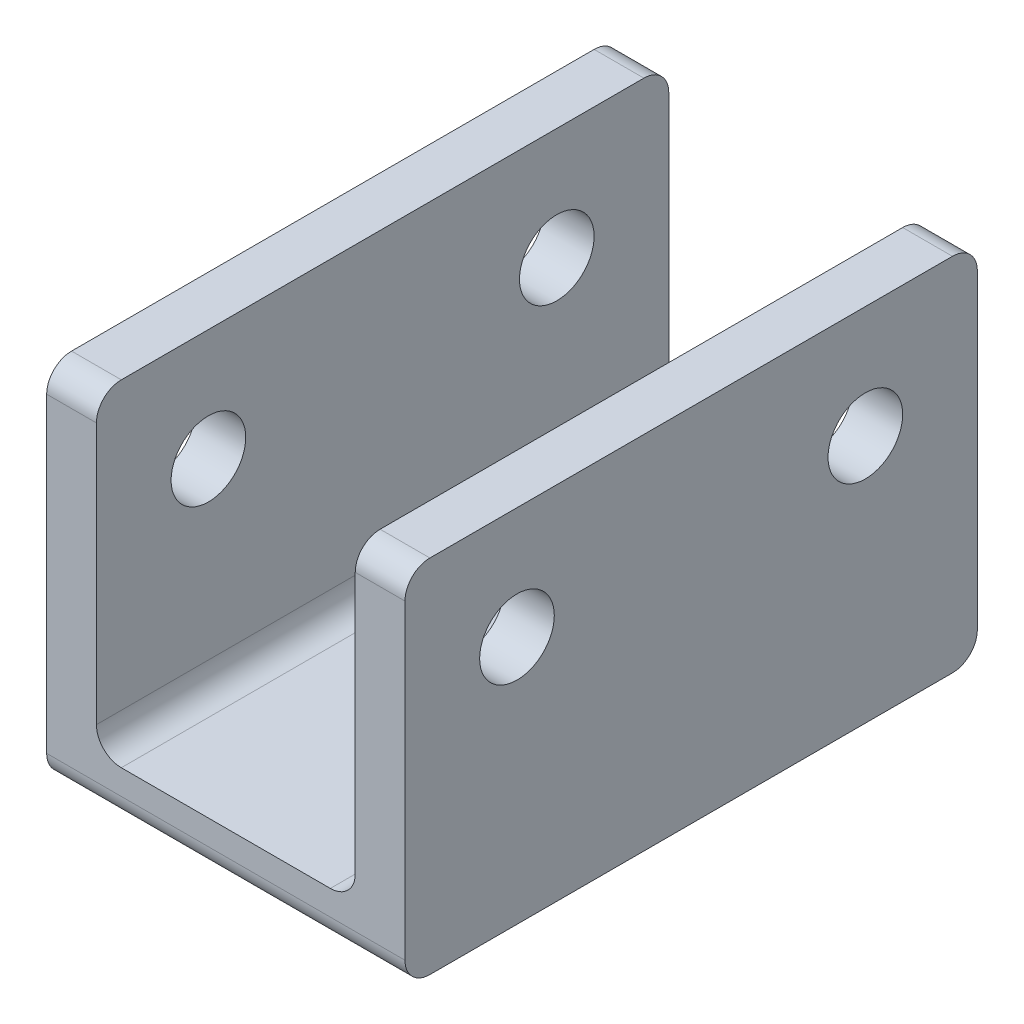
SolidWorks part; units mm, degrees
ref_plane "Front Plane" through (0, 0, 0) normal (0, 0, 1) x (1, 0, 0)
ref_plane "Top Plane" through (0, 0, 0) normal (0, 1, 0) x (1, 0, 0)
ref_plane "Right Plane" through (0, 0, 0) normal (1, 0, 0) x (0, 0, -1)
sketch "Sketch1" plane through (0, 0, 0) normal (0, 0, 1) x (1, 0, 0)
  line L0 (-5.2, 1) -> (5.2, 1)
  line L5 (7.2, -1) -> (-7.2, -1)
  line L6 (-5.2, 1) -> (-5.2, 13.5)
  line L7 (-5.2, 13.5) -> (-7.2, 13.5)
  line L8 (-7.2, 13.5) -> (-7.2, -1)
  line L9 (0, -55) -> (0, 55) construction
  line L10 (7.2, 13.5) -> (7.2, -1)
  line L11 (5.2, 13.5) -> (7.2, 13.5)
  line L12 (5.2, 1) -> (5.2, 13.5)
  point P2 (0, 1)
  point P16 (0, -1)
  dimension "D1" = 1
  dimension "D2" = 1
  dimension "D3" = 2
  dimension "D4" = 14.4
  dimension "D5" = 13.5
extrude "Boss-Extrude1" add sketch "Sketch1" along normal mid plane 23
sketch "Sketch2" plane through (7.2, 0, 0) normal (1, 0, 0) x (0, 0, -1)
  line L0 (0, 7.92) -> (0, -7.92) construction
  line L1 (-11.5, 13.5) -> (11.5, 13.5) construction
  circle A0 centre (-7, 9) radius 1.5
  circle A1 centre (7, 9) radius 1.5
  dimension "D3" = 3
  dimension "D1" = 14
  dimension "D2" = 4.5
extrude "Cut-Extrude1" cut sketch "Sketch2" against normal through all both and the other way through all
fillet "Fillet1" radius 1 2 edges at (0, -1, 11.5) (0, -1, -11.5)
fillet "Fillet2" radius 1 2 edges at (-5.2, 1, 0) (5.2, 1, 0)
fillet "Fillet3" radius 1 4 edges at (-6.2, 13.5, -11.5) (6.2, 13.5, -11.5) (-6.2, 13.5, 11.5) (6.2, 13.5, 11.5)
